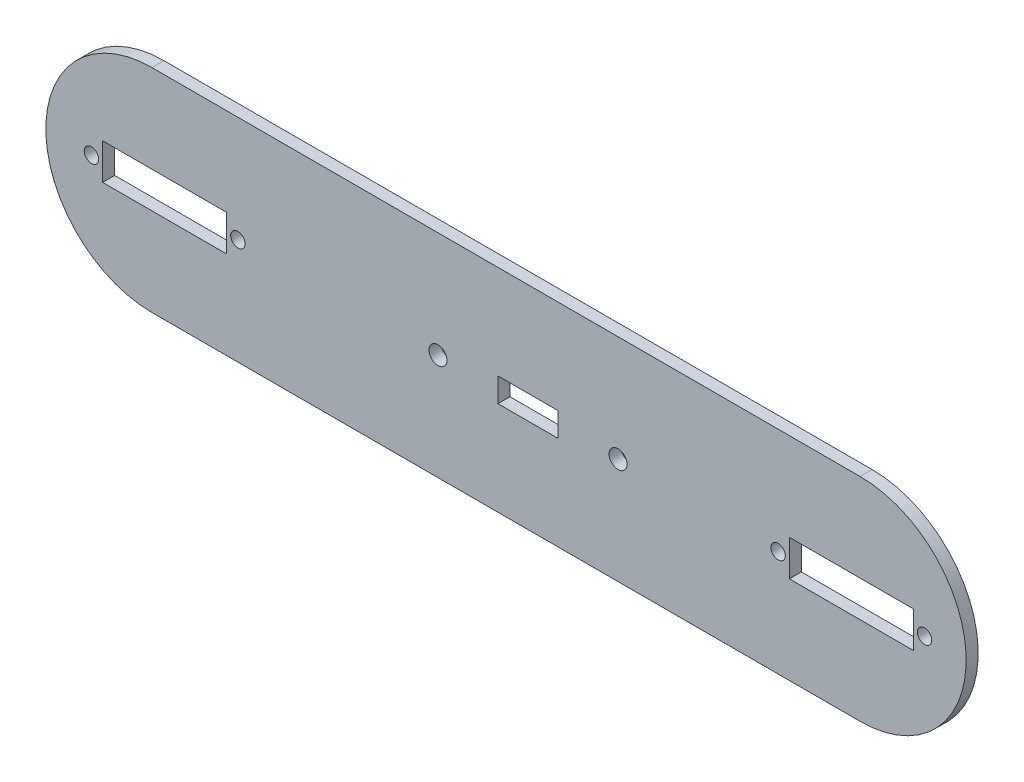
SolidWorks part; units mm, degrees
material "Balsa"
ref_plane "Plano frontal" through (0, 0, 0) normal (0, 0, 1) x (1, 0, 0)
ref_plane "Plano superior" through (0, 0, 0) normal (0, 1, 0) x (1, 0, 0)
ref_plane "Plano direito" through (0, 0, 0) normal (1, 0, 0) x (0, 0, -1)
sketch "Esboço1" plane through (0, 0, 0) normal (0, 0, 1) x (1, 0, 0)
  line L0 (-94, 26.5) -> (83, 26.5)
  line L1 (-94, -26.5) -> (83, -26.5)
  line L2 (-94, 0) -> (-20.25, 0) construction
  line L3 (-22.5, 0) -> (22.5, 0) construction
  line L4 (0, 11.6249) -> (0, -21.7831) construction
  line L6 (-109.1, 0) -> (-72.5, 0) construction
  line L7 (-7.5, -3) -> (7.5, -3)
  line L8 (-7.5, -3) -> (-7.5, 3)
  line L9 (-7.5, 3) -> (7.5, 3)
  line L10 (7.5, -3) -> (7.5, 3)
  line L11 (-7.5, -3) -> (7.5, 3) construction
  line L12 (-7.5, 3) -> (7.5, -3) construction
  line L13 (62.5, 0) -> (99.1, 0) construction
  line L14 (-106.3, -4.5) -> (-75.3, -4.5)
  line L16 (-106.3, 4.5) -> (-75.3, 4.5)
  line L17 (-75.3, -4.5) -> (-75.3, 4.5)
  line L18 (-106.3, -4.5) -> (-75.3, 4.5) construction
  line L19 (-106.3, 4.5) -> (-75.3, -4.5) construction
  line L21 (65.3, -4.5) -> (96.3, -4.5)
  line L22 (65.3, -4.5) -> (65.3, 4.5)
  line L23 (65.3, 4.5) -> (96.3, 4.5)
  line L24 (96.3, -4.5) -> (96.3, 4.5)
  line L25 (65.3, -4.5) -> (96.3, 4.5) construction
  line L26 (65.3, 4.5) -> (96.3, -4.5) construction
  line L27 (-106.3, 4.5) -> (-106.3, -4.5)
  arc A0 (83, -26.5) -> (83, 26.5) centre (83, 0) ccw
  arc A1 (-94, 26.5) -> (-94, -26.5) centre (-94, 0) ccw
  circle A4 centre (-22.5, 0) radius 2.25
  circle A5 centre (22.5, 0) radius 2.25
  circle A6 centre (-109.1, 0) radius 1.8
  circle A7 centre (-72.5, 0) radius 1.8
  circle A8 centre (62.5, 0) radius 1.8
  circle A9 centre (99.1, 0) radius 1.8
  point P8 (0, 0)
  point P19 (0, 0)
  point P29 (-90.8, 0)
  point P34 (80.8, 0)
  dimension "D1" = 4.5
  dimension "D5" = 15
  dimension "D6" = 26.5
  dimension "D7" = 3.6
  dimension "D2" = 45
  dimension "D3" = 83
  dimension "D4" = 94
  dimension "D8" = 36.6
  dimension "D9" = 50
  dimension "D10" = 6
  dimension "D11" = 9
  dimension "D12" = 31
  dimension "D13" = 40
extrude "Ressalto-extrusão1" add sketch "Esboço1" along normal blind 3
